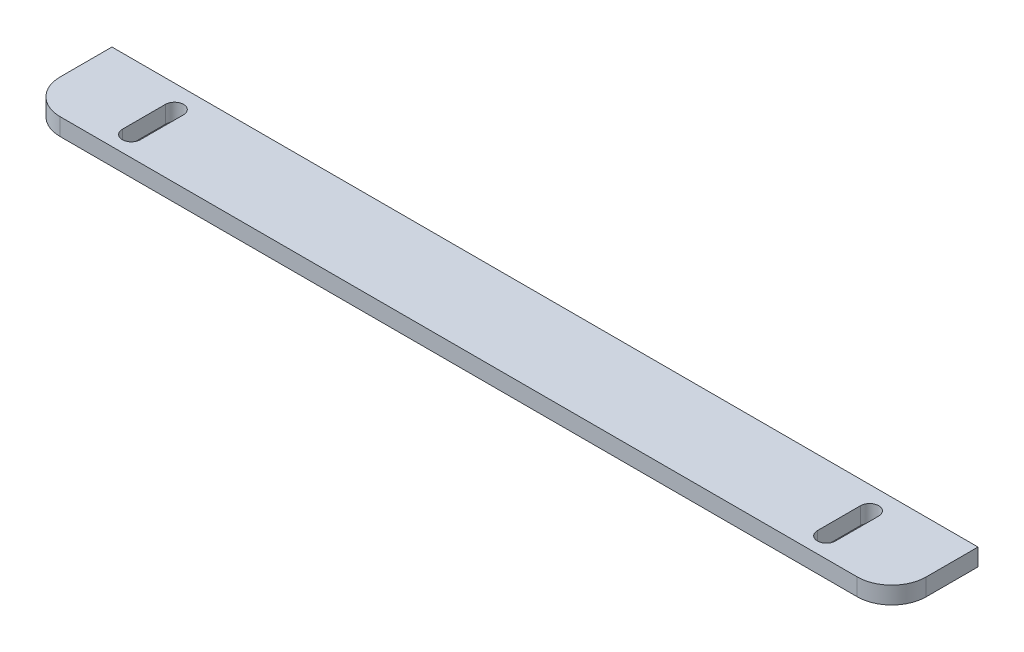
SolidWorks part; units mm, degrees
material "Acrílico (Impacto medio-alto)"
ref_plane "Alzado" through (0, 0, 0) normal (0, 0, 1) x (1, 0, 0)
ref_plane "Planta" through (0, 0, 0) normal (0, 1, 0) x (1, 0, 0)
ref_plane "Vista lateral" through (0, 0, 0) normal (1, 0, 0) x (0, 0, -1)
sketch "Croquis1" plane through (0, 0, 0) normal (0, 1, 0) x (1, 0, 0)
  line L0 (125.5, 25) -> (125.5, 0) construction
  line L1 (10, 0) -> (241, 0)
  line L2 (0, 10) -> (0, 25)
  line L3 (0, 25) -> (251, 25)
  line L4 (251, 10) -> (251, 25)
  line L5 (0, 17.5) -> (251, 17.5) construction
  line L6 (24.77, 25) -> (24.77, 0) construction
  line L7 (24.77, 18.3595) -> (24.77, 5.8595) construction
  line L8 (27.395, 18.3595) -> (27.395, 5.8595)
  line L9 (22.145, 18.3595) -> (22.145, 5.8595)
  line L10 (226.23, 25) -> (226.23, 0) construction
  line L11 (226.23, 18.3595) -> (226.23, 5.8595) construction
  line L12 (223.605, 18.3595) -> (223.605, 5.8595)
  line L13 (228.855, 18.3595) -> (228.855, 5.8595)
  arc A0 (27.395, 18.3595) -> (22.145, 18.3595) centre (24.77, 18.3595) ccw
  arc A1 (22.145, 5.8595) -> (27.395, 5.8595) centre (24.77, 5.8595) ccw
  arc A2 (223.605, 18.3595) -> (228.855, 18.3595) centre (226.23, 18.3595) cw
  arc A3 (228.855, 5.8595) -> (223.605, 5.8595) centre (226.23, 5.8595) cw
  arc A4 (10, 0) -> (0, 10) centre (10, 10) cw
  arc A5 (241, 0) -> (251, 10) centre (241, 10) ccw
  point P13 (24.77, 12.1095)
  point P22 (226.23, 12.1095)
  point P29 (0, 0)
  dimension "D3" = 100.73
  dimension "D6" = 5.8595
  dimension "D4" = 12.5
  dimension "D5" = 5.25
  dimension "D7" = 10
  dimension "D1" = 251
  dimension "D2" = 25
extrude "Saliente-Extruir1" add sketch "Croquis1" along normal blind 5
